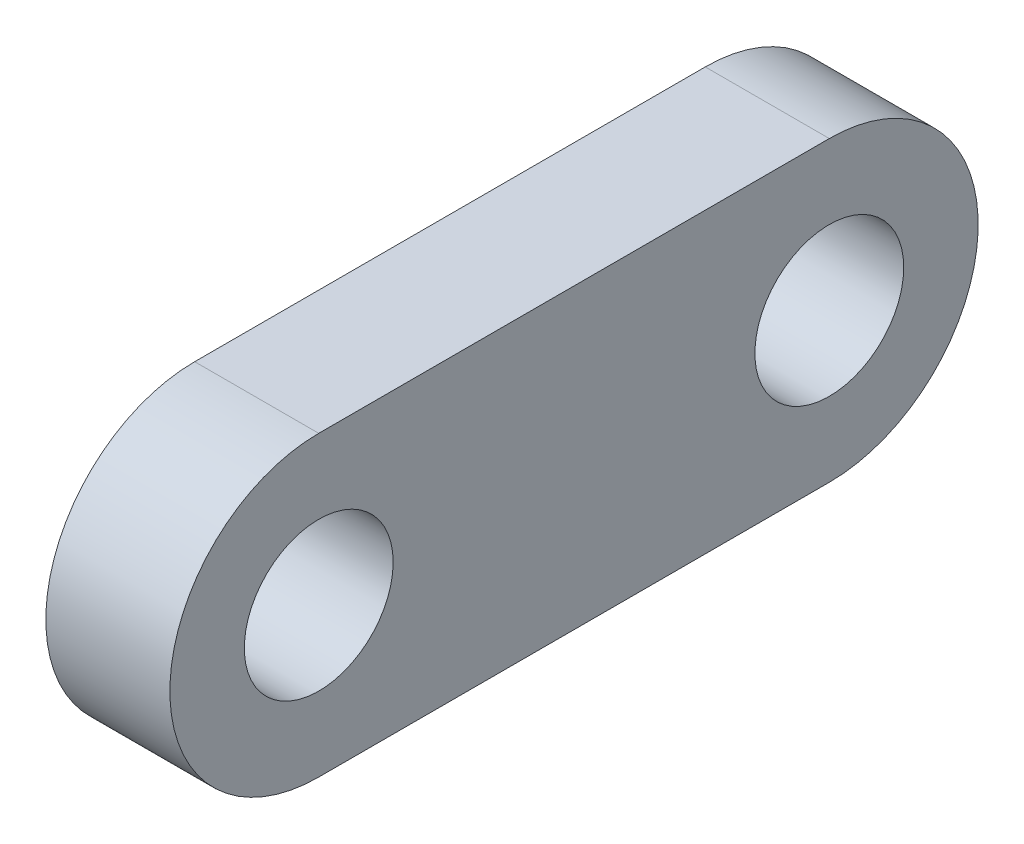
SolidWorks part; units mm, degrees
ref_plane "Plano frontal" through (0, 0, 0) normal (0, 0, 1) x (1, 0, 0)
ref_plane "Plano superior" through (0, 0, 0) normal (0, 1, 0) x (1, 0, 0)
ref_plane "Plano direito" through (0, 0, 0) normal (1, 0, 0) x (0, 0, -1)
sketch "Esboço1" plane through (0, 0, 0) normal (1, 0, 0) x (0, 0, -1)
  line L0 (-21.4349, 0) -> (-0.8549, 0) construction
  line L1 (-21.4349, 6) -> (-0.8549, 6)
  line L2 (-21.4349, -6) -> (-0.8549, -6)
  arc A0 (-21.4349, 6) -> (-21.4349, -6) centre (-21.4349, 0) ccw
  arc A1 (-0.8549, -6) -> (-0.8549, 6) centre (-0.8549, 0) ccw
  circle A2 centre (-21.4349, 0) radius 3
  circle A3 centre (-0.8549, 0) radius 3
  point P3 (-11.1449, 0)
  dimension "D2" = 6
  dimension "D3" = 6
  dimension "D4" = 6
  dimension "D1" = 20.58
extrude "Ressalto-extrusão1" add sketch "Esboço1" along normal blind 5
equation "\"D4@Esboço1\"=\"D3@Esboço1\""
